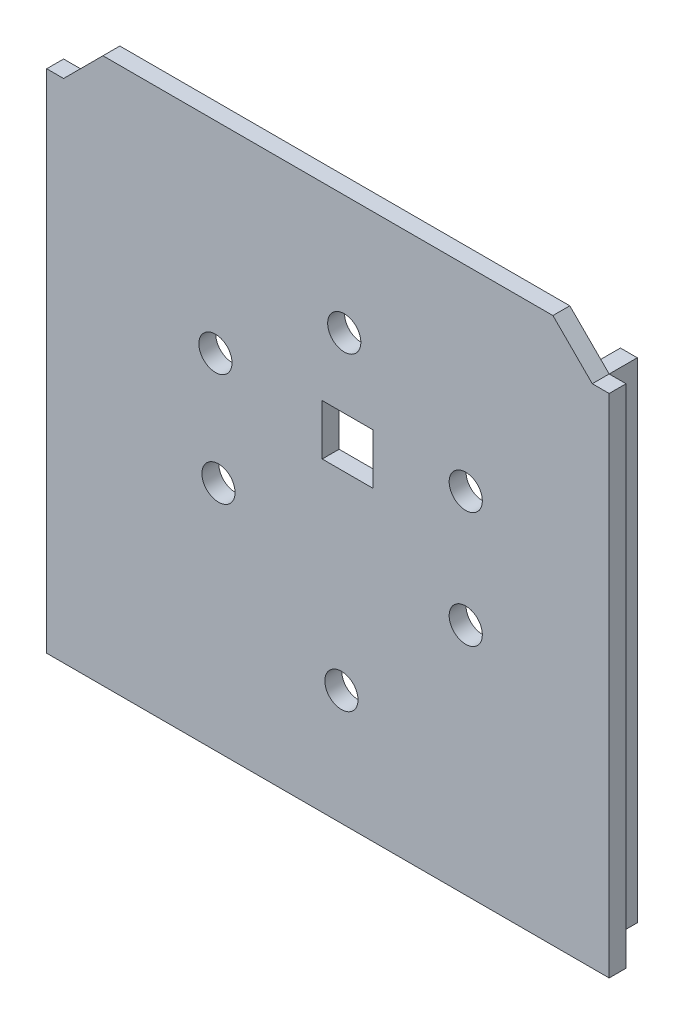
SolidWorks part; units mm, degrees
ref_plane "Alzado" through (0, 0, 0) normal (0, 0, 1) x (1, 0, 0)
ref_plane "Planta" through (0, 0, 0) normal (0, 1, 0) x (1, 0, 0)
ref_plane "Vista lateral" through (0, 0, 0) normal (1, 0, 0) x (0, 0, -1)
sketch "Croquis1" plane through (0, 0, -0.1563) normal (0, 0, 1) x (1, 0, 0)
  line L0 (51.2611, 62.9887) -> (44.2611, 69.9887)
  line L1 (-41.6389, 60.3887) -> (50.1611, 60.3887) construction
  line L2 (-41.6389, 60.3887) -> (-41.6389, -27.0113) construction
  line L3 (-41.6389, -27.0113) -> (50.1611, -27.0113) construction
  line L4 (50.1611, 60.3887) -> (50.1611, -27.0113) construction
  line L5 (3.2486, 27.3921) -> (12.2486, 27.3921)
  line L6 (3.2486, 27.3921) -> (3.2486, 36.3921)
  line L7 (3.2486, 36.3921) -> (12.2486, 36.3921)
  line L8 (12.2486, 27.3921) -> (12.2486, 36.3921)
  line L14 (-45.7389, 62.9887) -> (-45.7389, -27.0113)
  line L15 (-45.7389, -27.0113) -> (54.2611, -27.0113)
  line L16 (54.2611, 62.9887) -> (54.2611, -27.0113)
  line L17 (-35.7389, 69.9887) -> (44.2611, 69.9887)
  line L18 (-42.7389, 62.9887) -> (-35.7389, 69.9887)
  line L19 (51.2611, 62.9887) -> (54.2611, 62.9887)
  line L20 (-42.7389, 62.9887) -> (-45.7389, 62.9887)
  circle A0 centre (7.1611, 48.7704) radius 2.95
  circle A1 centre (28.7611, 35.1704) radius 2.95
  circle A2 centre (28.7611, 14.5704) radius 2.95
  circle A3 centre (6.6611, -6.5296) radius 2.95
  circle A4 centre (-15.1989, 14.4704) radius 2.95
  circle A5 centre (-15.7389, 34.1704) radius 2.95
  dimension "D1" = 5.9
  dimension "D2" = 100
  dimension "D3" = 90
  dimension "D4" = 3
  dimension "D5" = 3
  dimension "D6" = 7
  dimension "D7" = 135
  dimension "D8" = 135
extrude "Saliente-Extruir1" add sketch "Croquis1" along normal blind 3
sketch "Croquis9" plane through (0, 0, -0.1563) normal (0, 0, -1) x (-1, 0, 0)
  line L11 (-51.2611, 62.9887) -> (-48.2611, 62.9887)
  line L12 (-48.2611, 62.9887) -> (-48.2611, -21.0113)
  line L13 (-48.2611, -21.0113) -> (39.7389, -21.0113)
  line L14 (39.7389, -21.0113) -> (39.7389, 62.9887)
  line L15 (39.7389, 62.9887) -> (42.7389, 62.9887)
  line L16 (42.7389, 62.9887) -> (42.7389, -24.0113)
  line L17 (42.7389, -24.0113) -> (-51.2611, -24.0113)
  line L18 (-51.2611, -24.0113) -> (-51.2611, 62.9887)
  line L19 (45.7389, -27.0113) -> (-54.2611, -27.0113) construction
  dimension "D1" = 3
  dimension "D2" = 3
  dimension "D3" = 3
extrude "Saliente-Extruir6" add sketch "Croquis9" along normal blind 5
